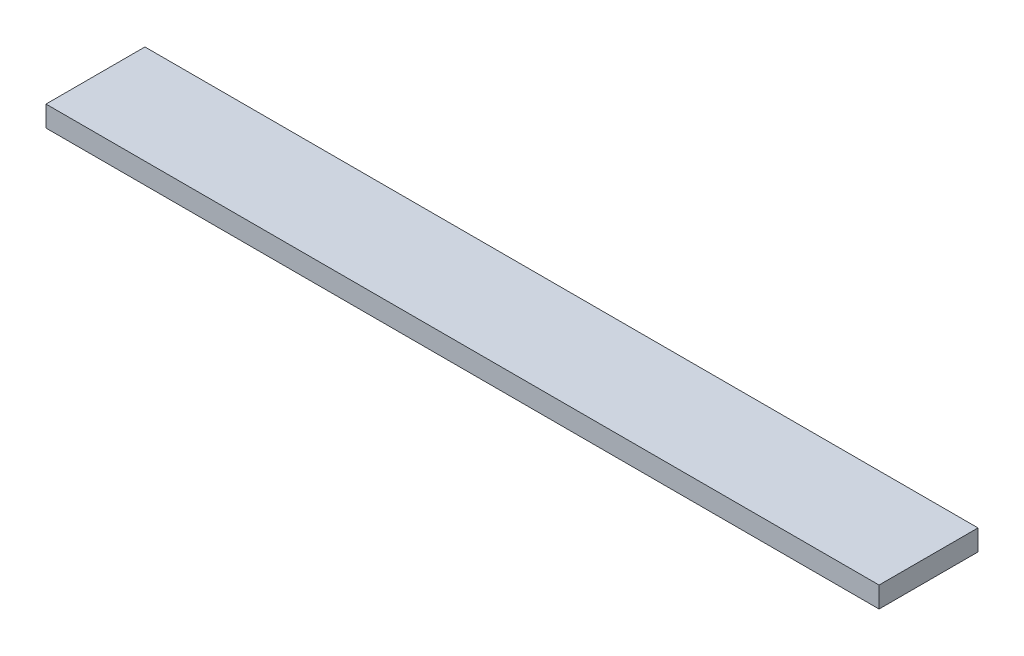
SolidWorks part; units mm, degrees
ref_plane "Front Plane" through (0, 0, 0) normal (0, 0, 1) x (1, 0, 0)
ref_plane "Top Plane" through (0, 0, 0) normal (0, 1, 0) x (1, 0, 0)
ref_plane "Right Plane" through (0, 0, 0) normal (1, 0, 0) x (0, 0, -1)
sketch "Sketch1" plane through (0, 0, 0) normal (0, 1, 0) x (1, 0, 0)
  line L1 (0, 0) -> (101.6, 0)
  line L2 (0, 0) -> (0, 12.065)
  line L3 (0, 12.065) -> (101.6, 12.065)
  line L4 (101.6, 0) -> (101.6, 12.065)
  dimension "D1" = 12.065
  dimension "D2" = 101.6
extrude "Boss-Extrude1" add sketch "Sketch1" along normal blind 2.54
